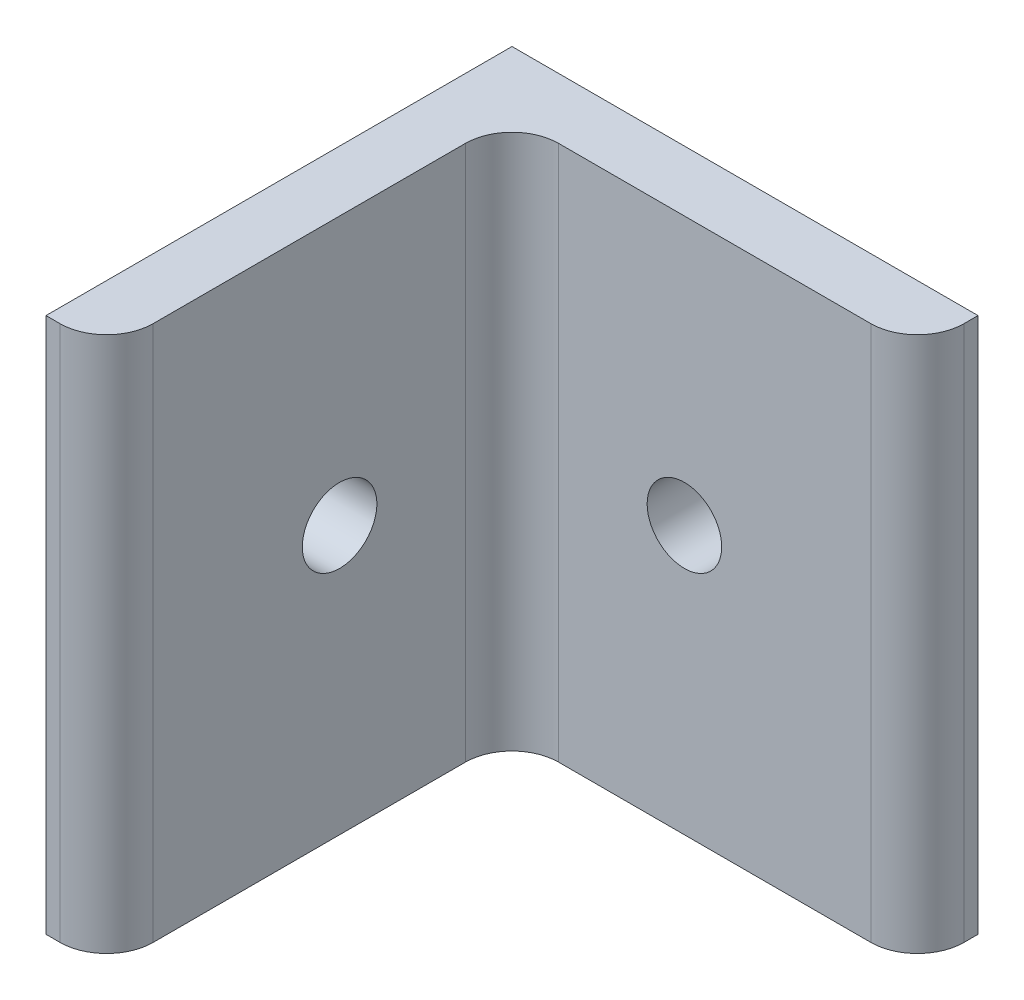
SolidWorks part; units mm, degrees
material "1060 Alloy"
ref_plane "Front Plane" through (0, 0, 0) normal (0, 0, 1) x (1, 0, 0)
ref_plane "Top Plane" through (0, 0, 0) normal (0, 1, 0) x (1, 0, 0)
ref_plane "Right Plane" through (0, 0, 0) normal (1, 0, 0) x (0, 0, -1)
sketch "Sketch1" plane through (0, 0, 0) normal (0, 1, 0) x (1, 0, 0)
  line L0 (0, 0) -> (0, -25.4)
  line L1 (0, -25.4) -> (3.302, -25.4)
  line L2 (3.302, -25.4) -> (3.302, -3.302)
  line L3 (3.302, -3.302) -> (25.4, -3.302)
  line L4 (25.4, -3.302) -> (25.4, 0)
  line L5 (25.4, 0) -> (0, 0)
  dimension "D1" = 3.302
  dimension "D3" = 25.4
extrude "Boss-Extrude1" add sketch "Sketch1" along normal blind 29.21
fillet "Fillet1" radius 2.54 3 edges at (3.302, 14.605, 25.4) (25.4, 14.605, 3.302) (3.302, 14.605, 3.302)
sketch "Sketch2" plane through (0, 0, 0) normal (-1, 0, 0) x (0, 0, 1)
  line L0 (25.4, 14.605) -> (0, 14.605) construction
  line L1 (25.4, 29.21) -> (25.4, 0) construction
  line L2 (0, 29.21) -> (0, 0) construction
  line L4 (0, 29.21) -> (25.4, 29.21) construction
  line L5 (12.7, 29.21) -> (12.7, 0) construction
  line L6 (0, 0) -> (25.4, 0) construction
  circle A0 centre (12.7, 14.605) radius 2.032
  dimension "D1" = 4.064
extrude "Cut-Extrude1" cut sketch "Sketch2" against normal through all
sketch "Sketch3" plane through (0, 0, 0) normal (0, 0, -1) x (-1, 0, 0)
  line L1 (-12.7, 29.21) -> (-12.7, 0) construction
  line L3 (-25.4, 0) -> (0, 0) construction
  line L5 (-25.4, 29.21) -> (0, 29.21) construction
  circle A0 centre (-12.7, 14.605) radius 2.032
  point P13 (-12.7, 0)
  dimension "D1" = 4.064
  dimension "D2" = 14.605
extrude "Cut-Extrude2" cut sketch "Sketch3" against normal through all
